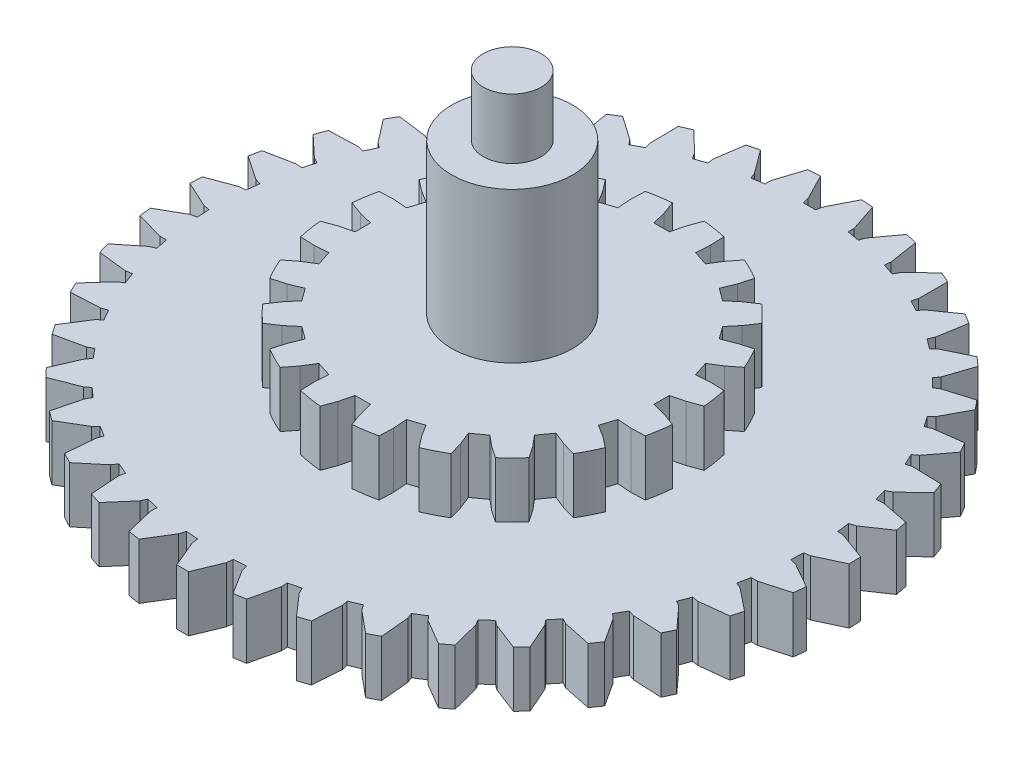
SolidWorks part; units mm, degrees
material "Gray Cast Iron"
ref_plane "Front Plane" through (0, 0, 0) normal (0, 0, 1) x (1, 0, 0)
ref_plane "Top Plane" through (0, 0, 0) normal (0, 1, 0) x (1, 0, 0)
ref_plane "Right Plane" through (0, 0, 0) normal (1, 0, 0) x (0, 0, -1)
sketch "Sketch2" plane through (0, 0, 0) normal (0, 1, 0) x (1, 0, 0)
  circle A0 centre (-91.1646, 64.6494) radius 16.256
extrude "Boss-Extrude1" add sketch "Sketch2" along normal blind 2.7432
sketch "Sketch3" plane through (0, 2.7432, 0) normal (0, 1, 0) x (1, 0, 0)
  circle A0 centre (-91.1646, 64.6494) radius 8.7186
extrude "Boss-Extrude2" add sketch "Sketch3" along normal blind 2.7432
sketch "Sketch4" plane through (0, 5.4864, 0) normal (0, 1, 0) x (1, 0, 0)
  circle A0 centre (-91.1646, 64.6494) radius 2.9845
extrude "Boss-Extrude3" add sketch "Sketch4" along normal blind 7.4168
sketch "Sketch5" plane through (0, 12.9032, 0) normal (0, 1, 0) x (1, 0, 0)
  circle A0 centre (-91.1646, 64.6494) radius 1.4288
extrude "Boss-Extrude4" add sketch "Sketch5" along normal blind 2.9718 contours A0
sketch "Sketch6" plane through (0, 0, 0) normal (0, -1, 0) x (1, 0, 0)
  circle A0 centre (-91.1646, -64.6494) radius 1.4288
extrude "Boss-Extrude5" add sketch "Sketch6" along normal blind 2.9718 contours A0
sketch "Sketch8" plane through (0, 2.7432, 0) normal (0, 1, 0) x (1, 0, 0)
  line L1 (-91.1646, 79.3052) -> (-90.8598, 79.3052)
  line L2 (-91.1646, 79.3052) -> (-91.4694, 79.3052)
  line L3 (-91.4694, 79.3052) -> (-91.5292, 79.6041)
  line L4 (-90.8598, 79.3052) -> (-90.8013, 79.6053)
  line L5 (-90.8013, 79.6053) -> (-90.1538, 80.874)
  line L6 (-90.1538, 80.874) -> (-90.1538, 81.7629)
  line L7 (-91.5292, 79.6041) -> (-92.1846, 80.8734)
  line L8 (-92.1846, 80.8734) -> (-92.1846, 81.5401)
  line L9 (-92.1846, 81.5401) -> (-90.1538, 81.7629)
  circle A0 centre (-91.1646, 64.6494) radius 16.256 construction
  dimension "D1" = 164
  dimension "D2" = 164
extrude "Cut-Extrude1" cut sketch "Sketch8" against normal through all
sketch "Sketch9" plane through (0, 15.875, 0) normal (0, 1, 0) x (1, 0, 0)
  line L0 (-91.1646, 64.6494) -> (-91.1646, 68.836)
  line L1 (-91.1646, 64.6494) -> (-96.2123, 64.6494)
pattern_circular "CirPattern15" count 39 over 360 about axis through (-91.1646, 0, -64.6494) along (0, 1, 0) of "Cut-Extrude1"
sketch "Sketch10" plane through (0, 5.4864, 0) normal (0, 1, 0) x (1, 0, 0)
  line L0 (-91.1646, 64.6494) -> (-91.1646, 73.368)
  line L1 (-91.1646, 72.018) -> (-91.5456, 72.018)
  line L2 (-91.1646, 72.018) -> (-90.7836, 72.018)
  line L3 (-91.5456, 72.018) -> (-91.7115, 72.6834)
  line L4 (-90.7836, 72.018) -> (-90.6177, 72.6834)
  line L5 (-91.7115, 72.6834) -> (-91.9479, 73.3327)
  line L6 (-90.6177, 72.6834) -> (-90.3814, 73.3327)
  line L7 (-90.3814, 73.3327) -> (-90.3079, 73.5834)
  line L8 (-90.3079, 73.5834) -> (-91.9479, 73.5207)
  line L9 (-91.9479, 73.5207) -> (-91.9479, 73.3327)
  circle A1 centre (-91.1646, 64.6494) radius 8.7186 construction
  circle A2 centre (-91.1646, 64.6494) radius 8.7186 construction
  dimension "D3" = 174
  dimension "D4" = 174
extrude "Cut-Extrude2" cut sketch "Sketch10" against normal blind 2.7432 contours L6 L7 L8 L9 L5 L3 L1 L2 L4
pattern_circular "CirPattern16" count 20 over 360 about axis through (-91.1646, 0, -64.6494) along (0, 1, 0) of "Cut-Extrude2"
